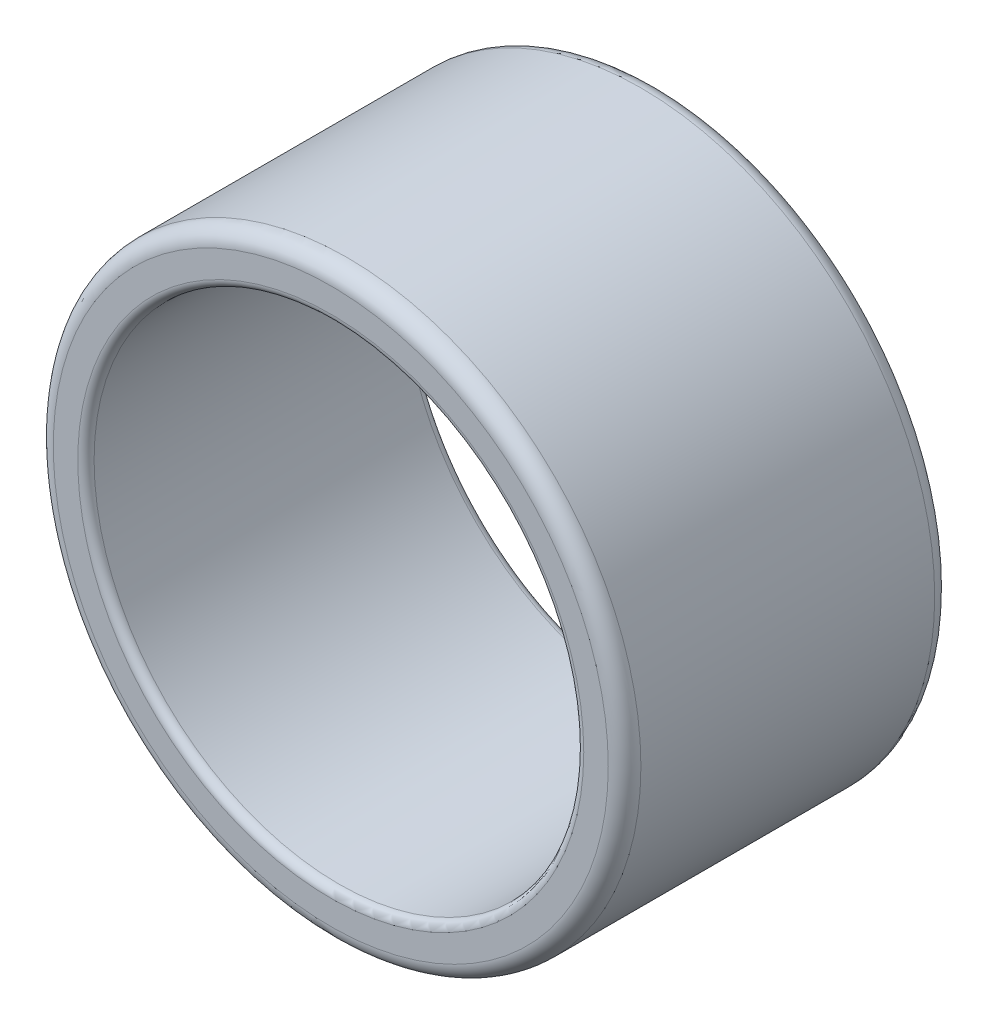
SolidWorks part; units mm, degrees
ref_plane "Ön Düzlem" through (0, 0, 0) normal (0, 0, 1) x (1, 0, 0)
ref_plane "Üst Düzlem" through (0, 0, 0) normal (0, 1, 0) x (1, 0, 0)
ref_plane "Sağ Düzlem" through (0, 0, 0) normal (1, 0, 0) x (0, 0, -1)
sketch "Çizim1" plane through (0, 0, 0) normal (0, 0, 1) x (1, 0, 0)
  circle A0 centre (0, 0) radius 180
extrude "Yükseklik-Ekstrüzyon1" add sketch "Çizim1" along normal blind 200
fillet "Radyus2" radius 10 2 edges at (180, 0, 0) (180, 0, 200)
sketch "Çizim2" plane through (0, 0, 0) normal (0, 0, -1) x (-1, 0, 0)
  circle A0 centre (0, 0) radius 150
extrude "Kes-Ekstrüzyon1" cut sketch "Çizim2" against normal blind 200
fillet "Radyus3" radius 5 2 edges at (-150, 0, 200) (-150, 0, 0)
